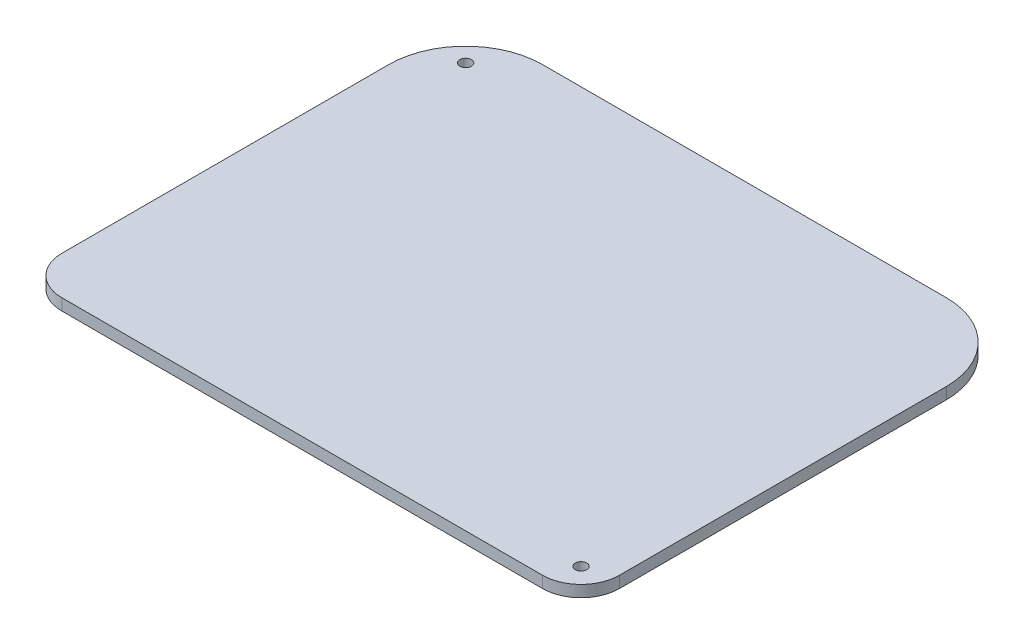
SolidWorks part; units mm, degrees
ref_plane "Front Plane" through (0, 0, 0) normal (0, 0, 1) x (1, 0, 0)
ref_plane "Top Plane" through (0, 0, 0) normal (0, 1, 0) x (1, 0, 0)
ref_plane "Right Plane" through (0, 0, 0) normal (1, 0, 0) x (0, 0, -1)
sketch "Sketch1" plane through (0, 0, 0) normal (0, 1, 0) x (1, 0, 0)
  line L2 (-72.5, 57.5) -> (72.5, 57.5)
  line L3 (-72.5, 57.5) -> (-72.5, -57.5)
  line L4 (-72.5, -57.5) -> (72.5, -57.5)
  line L5 (72.5, 57.5) -> (72.5, -57.5)
  line L6 (-72.5, 57.5) -> (72.5, -57.5) construction
  line L7 (-72.5, -57.5) -> (72.5, 57.5) construction
  point P0 (0, 0)
  dimension "D1" = 115
  dimension "D2" = 145
extrude "Boss-Extrude1" add sketch "Sketch1" along normal blind 3
fillet "Fillet1" radius 10 2 edges at (72.5, 1.5, 57.5) (-72.5, 1.5, 57.5)
fillet "Fillet2" radius 20 2 edges at (72.5, 1.5, -57.5) (-72.5, 1.5, -57.5)
sketch "Sketch2" plane through (0, 0, 0) normal (0, -1, 0) x (1, 0, 0)
  line L1 (-72.5, -37.5) -> (-72.5, 47.5) construction
  line L2 (52.5, -57.5) -> (-52.5, -57.5) construction
  line L3 (72.5, 47.5) -> (72.5, -37.5) construction
  line L4 (-62.5, 57.5) -> (62.5, 57.5) construction
  circle A0 centre (65.5, 50.5) radius 1.5
  circle A1 centre (-62.8681, -47.8673) radius 1.5
  point P6 (0, 0)
  dimension "D1" = 9.6319
  dimension "D2" = 9.6327
  dimension "D3" = 7
  dimension "D4" = 7
extrude "Cut-Extrude1" cut sketch "Sketch2" against normal up to next
